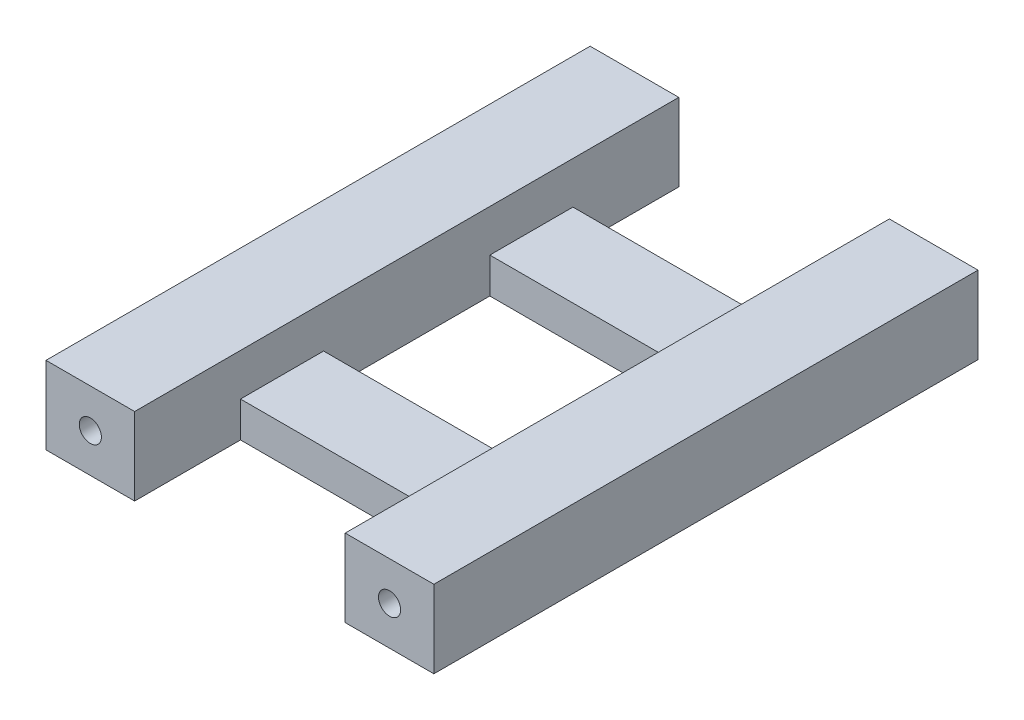
SolidWorks part; units mm, degrees
ref_plane "Alzado" through (0, 0, 0) normal (0, 0, 1) x (1, 0, 0)
ref_plane "Planta" through (0, 0, 0) normal (0, 1, 0) x (1, 0, 0)
ref_plane "Vista lateral" through (0, 0, 0) normal (1, 0, 0) x (0, 0, -1)
sketch "Croquis1" plane through (0, 0, 0) normal (0, 1, 0) x (1, 0, 0)
  line L0 (-10.4076, 7.3865) -> (8.5924, 7.3865)
  line L1 (-10.4076, 7.3865) -> (-10.4076, -7.6135)
  line L2 (-10.4076, -7.6135) -> (8.5924, -7.6135)
  line L3 (8.5924, 7.3865) -> (8.5924, -7.6135)
  line L4 (16.5924, -24.6635) -> (16.5924, 24.4365)
  line L5 (16.5924, 24.4365) -> (8.5924, 24.4365)
  line L6 (8.5924, 24.4365) -> (8.5924, 14.8865)
  line L7 (8.5924, 14.8865) -> (-10.4076, 14.8865)
  line L8 (-10.4076, 14.8865) -> (-10.4076, 24.4365)
  line L9 (-10.4076, 24.4365) -> (-18.4076, 24.4365)
  line L10 (-18.4076, 24.4365) -> (-18.4076, -24.6635)
  line L11 (-18.4076, -24.6635) -> (-10.4076, -24.6635)
  line L12 (-10.4076, -24.6635) -> (-10.4076, -15.1135)
  line L13 (-10.4076, -15.1135) -> (8.5924, -15.1135)
  line L14 (8.5924, -15.1135) -> (8.5924, -24.6635)
  line L15 (8.5924, -24.6635) -> (16.5924, -24.6635)
extrude "Saliente-Extruir1" add sketch "Croquis1" along normal blind 7
sketch "Croquis3" plane through (0, 0, 15.1135) normal (0, 0, 1) x (1, 0, 0)
  line L1 (-10.4076, 7) -> (8.5924, 7)
  line L2 (-10.4076, 7) -> (-10.4076, 3.2)
  line L3 (-10.4076, 3.2) -> (8.5924, 3.2)
  line L4 (8.5924, 7) -> (8.5924, 3.2)
  point P5 (0, 0)
  dimension "D1" = 3.8
extrude "Cortar-Extruir1" cut sketch "Croquis3" against normal blind 37.9
sketch "Croquis4" plane through (0, 0, 24.6635) normal (0, 0, 1) x (1, 0, 0)
  line L0 (-18.4076, 0) -> (-10.4076, 0) construction
  line L1 (8.5924, 0) -> (16.5924, 0) construction
  line L2 (-18.4076, 7) -> (-18.4076, 0) construction
  circle A0 centre (12.5924, 3.5) radius 1
  circle A1 centre (-14.4076, 3.5) radius 1
  point P4 (0, 0)
  point P5 (0, 0)
  point P8 (-14.4076, 0)
  point P9 (0, 0)
  point P12 (12.5924, 0)
  point P15 (-18.4076, 3.5)
  point P16 (0, 0)
  dimension "D1" = 2
extrude "Cortar-Extruir2" cut sketch "Croquis4" against normal blind 51.9
